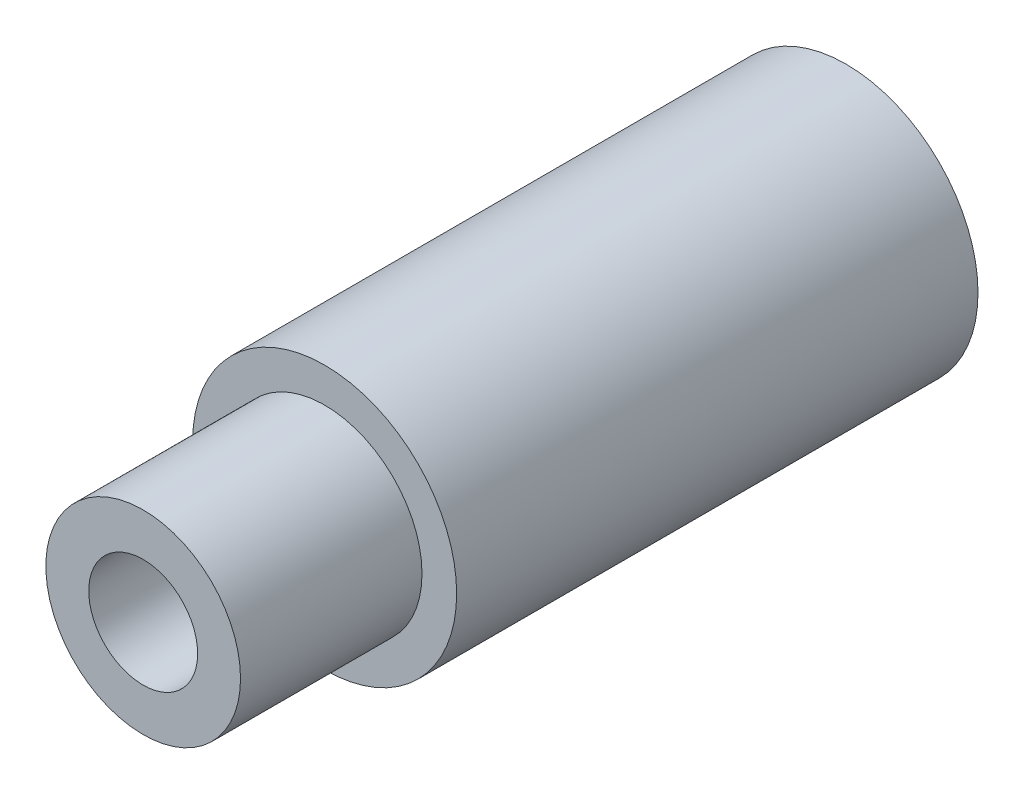
SolidWorks part; units mm, degrees
ref_plane "正面" through (0, 0, 0) normal (0, 0, 1) x (1, 0, 0)
ref_plane "平面" through (0, 0, 0) normal (0, 1, 0) x (1, 0, 0)
ref_plane "右側面" through (0, 0, 0) normal (1, 0, 0) x (0, 0, -1)
sketch "ｽｹｯﾁ1" plane through (0, 0, 0) normal (0, 0, 1) x (1, 0, 0)
  circle A0 centre (0, 0) radius 4
  dimension "D1" = 8
extrude "ﾎﾞｽ - 押し出し1" add sketch "ｽｹｯﾁ1" along normal mid plane 15.8
sketch "ｽｹｯﾁ2" plane through (0, 0, 7.9) normal (0, 0, 1) x (1, 0, 0)
  circle A0 centre (0, 0) radius 2.95
  dimension "D1" = 5.9
extrude "ﾎﾞｽ - 押し出し2" add sketch "ｽｹｯﾁ2" along normal blind 5.5
sketch "ｽｹｯﾁ3" plane through (0, 0, 13.4) normal (0, 0, 1) x (1, 0, 0)
  circle A0 centre (0, 0) radius 1.3614
sketch "ｽｹｯﾁ4" plane through (0, 0, -7.9) normal (0, 0, -1) x (-1, 0, 0)
  circle A0 centre (0, 0) radius 1.7134
hole_wizard "M4x0.7 ねじ穴1" positions "3Dｽｹｯﾁ3" profile "ｽｹｯﾁ6" tap size "M4x0.7" standard "JIS"
sketch3d "3Dｽｹｯﾁ3"
  point P0 (0, 0, -7.9)
  point P3 (0, 0, 13.4)
sketch "ｽｹｯﾁ6" plane through (0, 0, -7.9) normal (1, 0, 0) x (0, 1, 0)
  line L0 (0, 0) -> (0, 7.9914)
  line L1 (0, 7.9914) -> (1.65, 7)
  line L2 (1.65, 7) -> (1.65, 0)
  line L5 (1.65, 0) -> (0, 0)
  line L10 (0, 7.9914) -> (-1.65, 7) construction
  line L11 (0, -6.35) -> (0, 107.95) construction
  dimension "ねじ下穴ﾄﾞﾘﾙ直径" = 3.3
  dimension "ねじ下穴ﾄﾞﾘﾙの深さ" = 7
  dimension "ﾄﾞﾘﾙ角度" = 118
cosmetic thread "穴のねじ山1" parameters "D1"=5, "D2"=4
cosmetic thread "穴のねじ山2" parameters "D1"=5, "D2"=4
